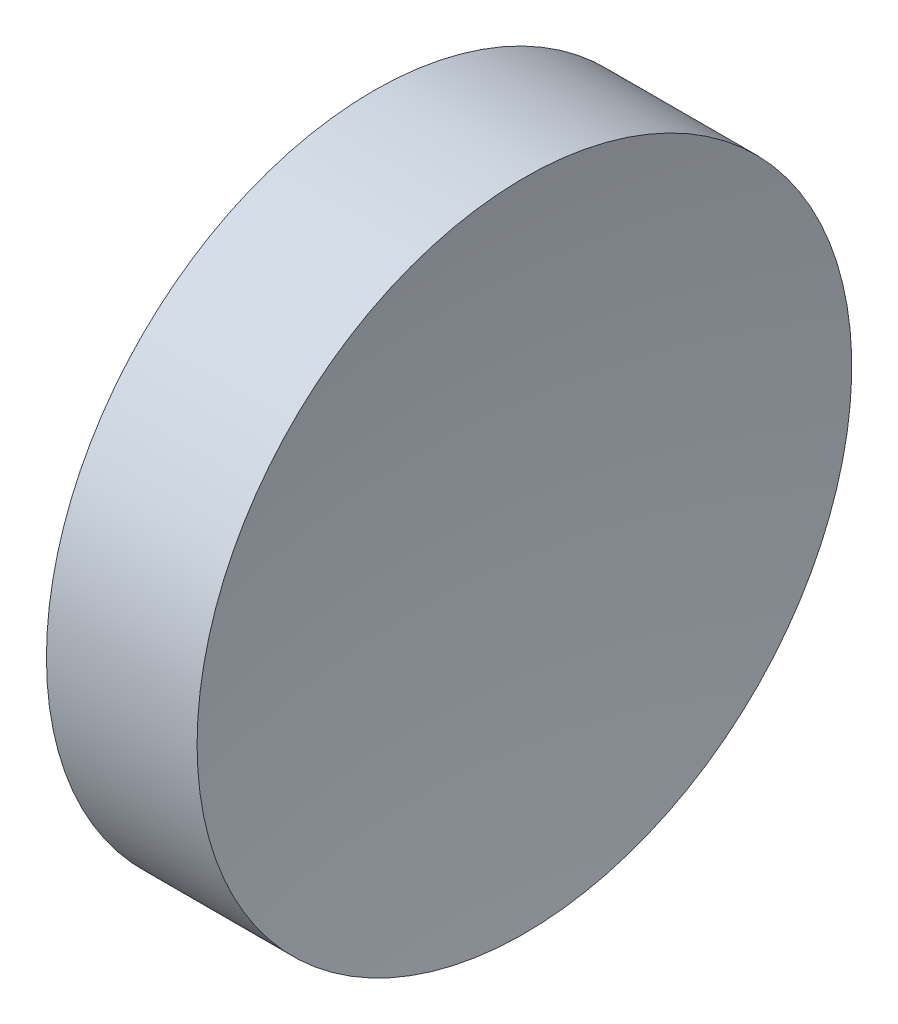
SolidWorks part; units mm, degrees
ref_plane "前视基准面" through (0, 0, 0) normal (0, 0, 1) x (1, 0, 0)
ref_plane "上视基准面" through (0, 0, 0) normal (0, 1, 0) x (1, 0, 0)
ref_plane "右视基准面" through (0, 0, 0) normal (1, 0, 0) x (0, 0, -1)
sketch "草图1" plane through (0, 0, 0) normal (0, 0, 1) x (1, 0, 0)
  line L0 (109.9369, 65.2226) -> (130.1809, 65.2226) construction
  line L1 (118.3527, 65.2226) -> (121.8527, 65.2226)
  line L3 (119.9713, 77.9226) -> (123.0287, 77.9226)
  line L4 (119.9713, 77.9226) -> (117.1842, 77.9226)
  arc A0 (118.3527, 65.2226) -> (117.1842, 77.9226) centre (48.7527, 65.2226) ccw
  arc A1 (123.0287, 77.9226) -> (121.8527, 65.2226) centre (191.4527, 65.182) ccw
revolve "旋转1" add sketch "草图1" angle 360 about L0
